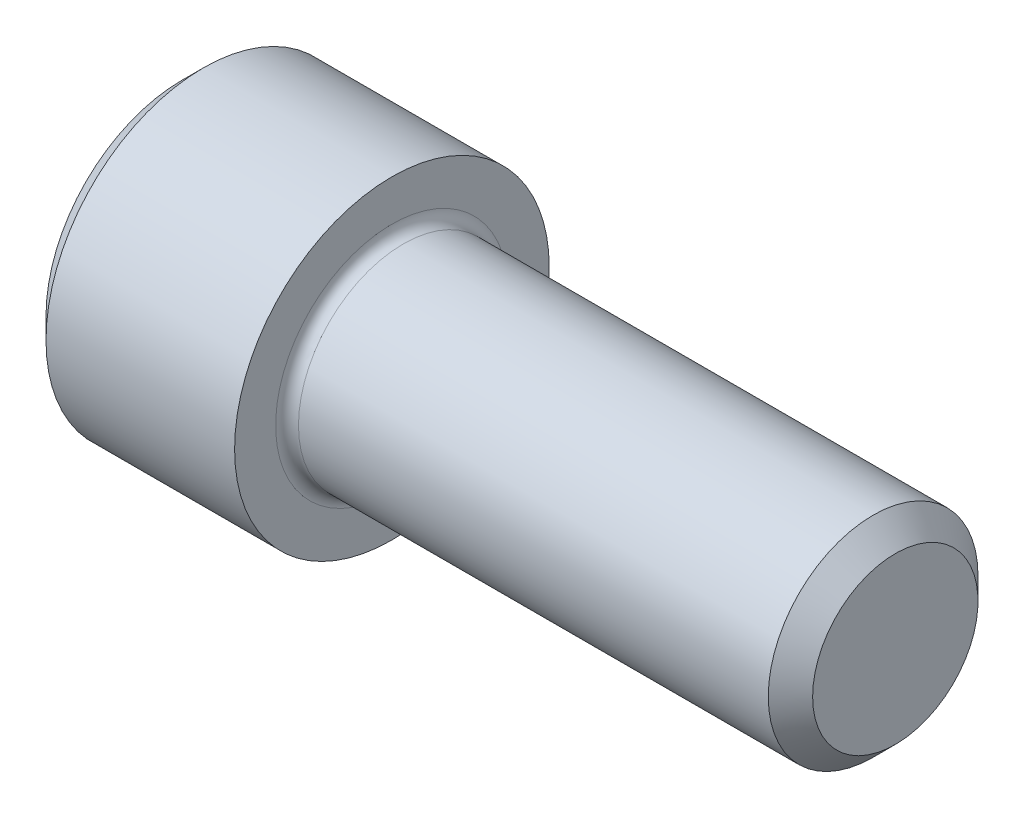
SolidWorks part; units mm, degrees
material "Plain Carbon Steel"
ref_plane "Plane1" through (0, 0, 0) normal (0, 0, 1) x (1, 0, 0)
ref_plane "Plane2" through (0, 0, 0) normal (0, 1, 0) x (1, 0, 0)
ref_plane "Plane3" through (0, 0, 0) normal (1, 0, 0) x (0, 0, -1)
sketch "BodySke" plane through (0, 0, 0) normal (0, 0, 1) x (1, 0, 0)
  line L0 (0, 0) -> (0, 5.1537)
  line L1 (0.8001, 5.9538) -> (7.9375, 5.9538)
  line L2 (7.9375, 5.9538) -> (7.9375, 3.9687)
  line L3 (7.9375, 3.9687) -> (26.148, 3.9687)
  line L4 (26.9875, 3.1293) -> (26.9875, 0)
  line L5 (26.9875, 0) -> (0, 0)
  line L6 (-31.75, 0) -> (127, 0) construction
  line L7 (0, 5.1537) -> (0.8001, 5.9538)
  line L8 (26.9875, 3.1293) -> (26.148, 3.9687)
  line L9 (0, -5.1537) -> (0.8001, -5.9538) construction
  line L10 (26.9875, -3.1293) -> (26.148, -3.9688) construction
  line L11 (9.3472, 9.525) -> (9.3472, 3.175) construction
  line L12 (7.9375, 9.525) -> (7.9375, 3.175) construction
  line L13 (-11.1125, 9.525) -> (-11.1125, 3.175) construction
  dimension "Diameter" = 7.9375
  dimension "Head_ht" = 7.9375
  dimension "Length" = 19.05
  dimension "Body_ch_ang" = 45
  dimension "Head_dia" = 11.9075
  dimension "Head_ch_ang" = 45
  dimension "Head_side_ht" = 7.1374
  dimension "Minor_dia" = 6.2586
  dimension "Advance" = 1.4097
  dimension "Thread_nom" = 19.05
  dimension "Thread_length" = 38.1
revolve "Base-Revolve" add sketch "BodySke"
cosmetic thread "ThreadCosmetic" [suppressed]
fillet "Fillet1" radius 0.4318 1 edges at (7.9375, 0, 3.9687)
sketch "Sketch2" plane through (0, 0, 0) normal (0, 0, 1) x (1, 0, 0)
  line L0 (0, 3.175) -> (3.8354, 3.175)
  line L1 (3.8354, 3.175) -> (5.6685, 0)
  line L2 (-31.75, 0) -> (127, 0) construction
  line L3 (5.6685, 0) -> (0, 0)
  line L4 (0, 0) -> (0, 3.175)
  line L5 (0, 5.1537) -> (0, -5.1537) construction
  line L6 (0, 0) -> (47.625, 0) construction
  line L7 (7.9375, -5.9538) -> (7.9375, 5.9538) construction
  dimension "D1" = 3.175
  dimension "D2" = 60
  dimension "Wall_thickness" = 4.1021
revolve "Hex-PreBroach" cut sketch "Sketch2" angle 360 about L6
sketch "Sketch3" plane through (0, 0, 0) normal (-1, 0, 0) x (0, 0.5, 0.866)
  line L0 (1.8331, 3.175) -> (-1.8331, 3.175)
  line L1 (-1.8331, 3.175) -> (-3.6662, 0)
  line L2 (1.8331, 3.175) -> (3.6662, 0)
  line L3 (1.8331, -3.175) -> (3.6662, 0)
  line L4 (1.8331, -3.175) -> (-1.8331, -3.175)
  line L5 (-1.8331, -3.175) -> (-3.6662, 0)
  dimension "D1" = 3.175
  dimension "D2" = 3.175
  dimension "Hex_size" = 6.35
extrude "Hex" cut sketch "Sketch3" against normal blind 3.8354
